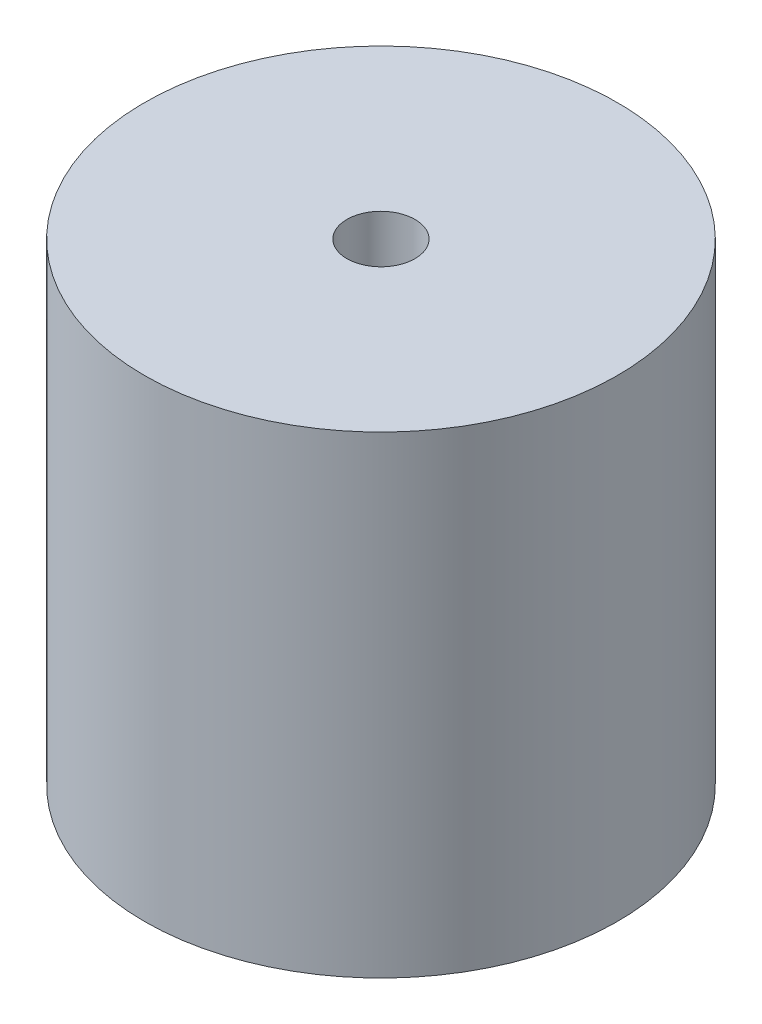
SolidWorks part; units mm, degrees
material "Alloy Steel (SS)"
ref_plane "Front Plane" through (0, 0, 0) normal (0, 0, 1) x (1, 0, 0)
ref_plane "Top Plane" through (0, 0, 0) normal (0, 1, 0) x (1, 0, 0)
ref_plane "Right Plane" through (0, 0, 0) normal (1, 0, 0) x (0, 0, -1)
sketch "Sketch1" plane through (0, 0, 0) normal (0, 1, 0) x (1, 0, 0)
  circle A0 centre (0, 0) radius 1.8288
  circle A1 centre (0, 0) radius 12.7
  dimension "D1" = 3.6576
  dimension "D2" = 25.4
extrude "Boss-Extrude1" add sketch "Sketch1" along normal blind 25.4
